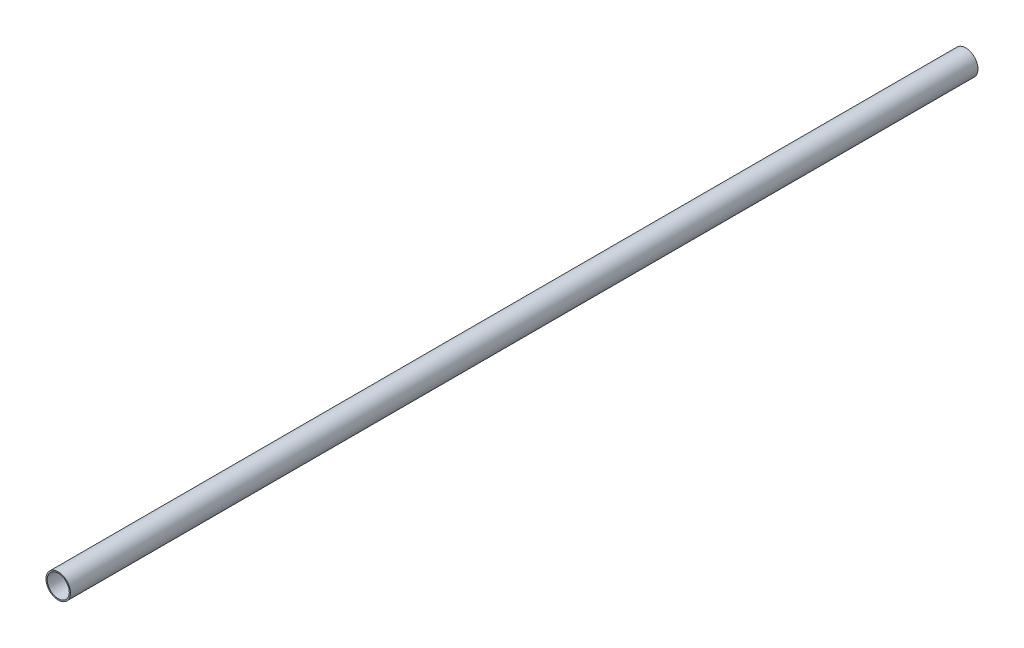
SolidWorks part; units mm, degrees
material "carbon fiber"
ref_plane "Front Plane" through (0, 0, 0) normal (0, 0, 1) x (1, 0, 0)
ref_plane "Top Plane" through (0, 0, 0) normal (0, 1, 0) x (1, 0, 0)
ref_plane "Right Plane" through (0, 0, 0) normal (1, 0, 0) x (0, 0, -1)
sketch "Эскиз1" plane through (0, 0, 0) normal (0, 0, 1) x (1, 0, 0)
  circle A0 centre (0, 0) radius 5
  circle A1 centre (0, 0) radius 4.5
  dimension "D1" = 10
  dimension "D2" = 0.5
extrude "Бобышка-Вытянуть1" add sketch "Эскиз1" along normal mid plane 370
